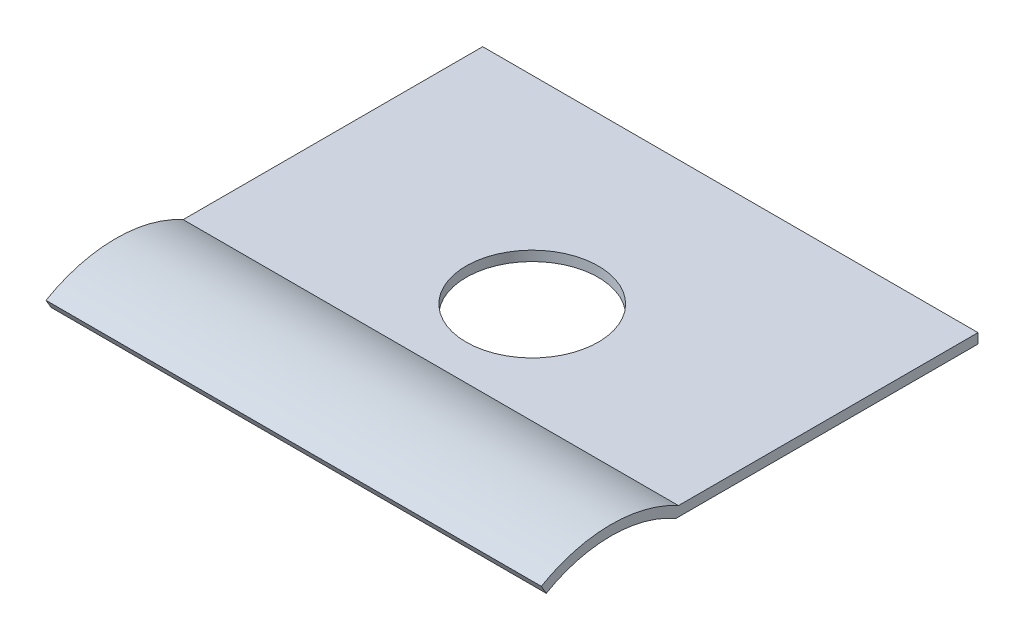
SolidWorks part; units mm, degrees
material "Alumina"
ref_plane "Front Plane" through (0, 0, 0) normal (0, 0, 1) x (1, 0, 0)
ref_plane "Top Plane" through (0, 0, 0) normal (0, 1, 0) x (1, 0, 0)
ref_plane "Right Plane" through (0, 0, 0) normal (1, 0, 0) x (0, 0, -1)
sketch "Sketch3" plane through (0, 0, 0) normal (1, 0, 0) x (0, 0, -1)
  line L0 (3.925, 0) -> (13.075, 0)
  line L1 (4.0038, 0.3) -> (13.075, 0.3)
  line L2 (-0.15, 0.2598) -> (0, 0)
  line L3 (13.075, 0.3) -> (13.075, 0)
  arc A0 (0, 0) -> (3.925, 0) centre (1.9625, -3.3991) cw
  arc A1 (-0.15, 0.2598) -> (4.0038, 0.3) centre (1.9625, -3.3991) cw
  dimension "D1" = 3.925
  dimension "D2" = 9.15
  dimension "D3" = 3.925
  dimension "D4" = 0.3
extrude "Boss-Extrude1" add sketch "Sketch3" along normal blind 15
sketch "Sketch4" plane through (0, 0.3, 0) normal (0, 1, 0) x (1, 0, 0)
  line L12 (0, 13.075) -> (0, 4.0038) construction
  line L13 (15, 13.075) -> (0, 13.075) construction
  line L14 (7.5, 13.075) -> (7.5, 7.075) construction
  circle A0 centre (7.5, 7.075) radius 2
  point P12 (7.5, 7.075)
  dimension "D4" = 4
  dimension "D1" = 7.5
  dimension "D2" = 6
extrude "Cut-Extrude1" cut sketch "Sketch4" against normal through all
